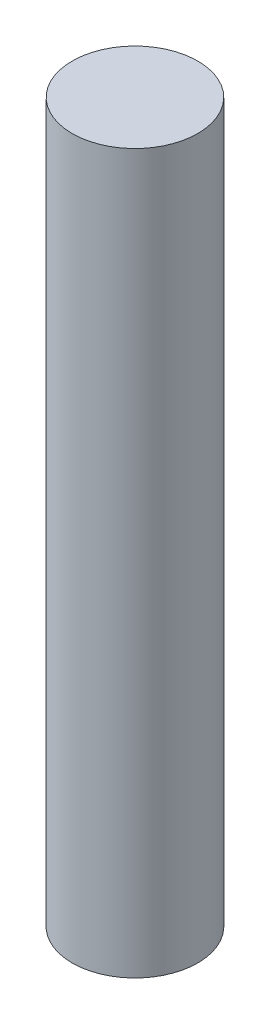
SolidWorks part; units mm, degrees
ref_plane "Front Plane" through (0, 0, 0) normal (0, 0, 1) x (1, 0, 0)
ref_plane "Top Plane" through (0, 0, 0) normal (0, 1, 0) x (1, 0, 0)
ref_plane "Right Plane" through (0, 0, 0) normal (1, 0, 0) x (0, 0, -1)
sketch "Sketch2" plane through (0, 0, 0) normal (0, 1, 0) x (1, 0, 0)
  circle A0 centre (0, 0) radius 13.115
  dimension "D1" = 26.23
extrude "Boss-Extrude1" add sketch "Sketch2" along normal mid plane 150
